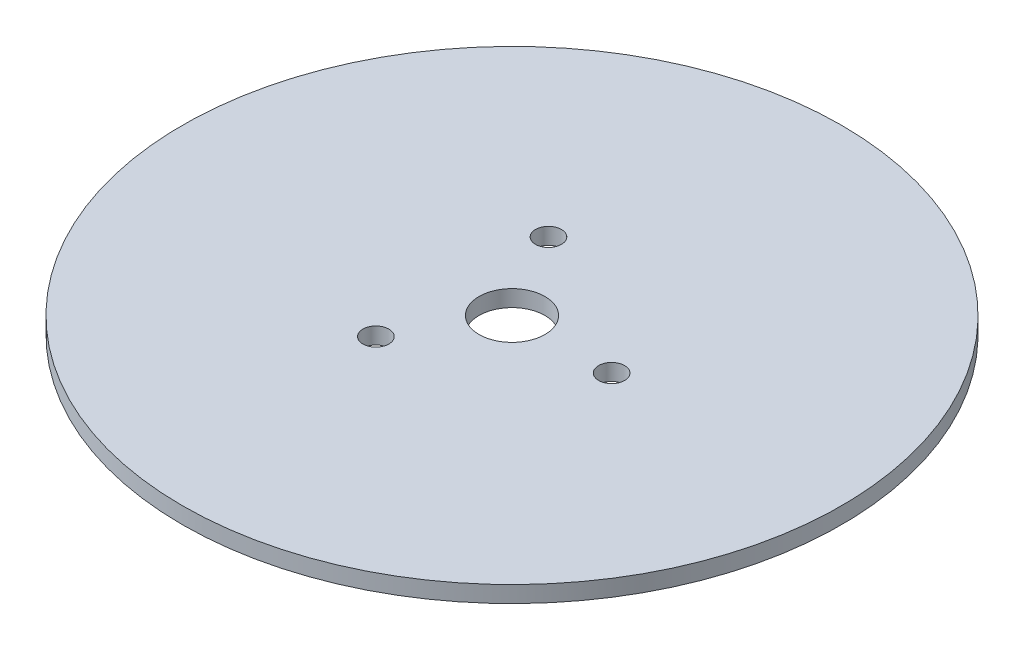
SolidWorks part; units mm, degrees
material "Acrylic (Medium-high impact)"
ref_plane "Front Plane" through (0, 0, 0) normal (0, 0, 1) x (1, 0, 0)
ref_plane "Top Plane" through (0, 0, 0) normal (0, 1, 0) x (1, 0, 0)
ref_plane "Right Plane" through (0, 0, 0) normal (1, 0, 0) x (0, 0, -1)
sketch "Sketch1" plane through (0, 0, 0) normal (0, 1, 0) x (1, 0, 0)
  line L0 (13, 0) -> (25.4, 0) construction
  line L2 (19.2, 0) -> (9.6, 16.6277) construction
  line L3 (9.6, 16.6277) -> (-9.6, 16.6277) construction
  line L4 (-9.6, 16.6277) -> (-19.2, 0) construction
  line L5 (-19.2, 0) -> (-9.6, -16.6277) construction
  line L6 (-9.6, -16.6277) -> (9.6, -16.6277) construction
  line L7 (9.6, -16.6277) -> (19.2, 0) construction
  circle A0 centre (0, 0) radius 63.5
  circle A1 centre (0, 0) radius 25.4 construction
  circle A2 centre (0, 0) radius 13 construction
  circle A3 centre (19.2, 0) radius 2.5
  circle A4 centre (0, 0) radius 16.6277 construction
  circle A5 centre (-9.6, 16.6277) radius 2.5
  circle A6 centre (-9.6, -16.6277) radius 2.5
  circle A7 centre (0, 0) radius 6.35
  dimension "D1" = 127
  dimension "D2" = 50.8
  dimension "D3" = 26
  dimension "D4" = 5
  dimension "D5" = 5
  dimension "D6" = 5
  dimension "D7" = 12.7
  dimension "D8" = 19.2
extrude "Boss-Extrude1" add sketch "Sketch1" along normal blind 3.175
